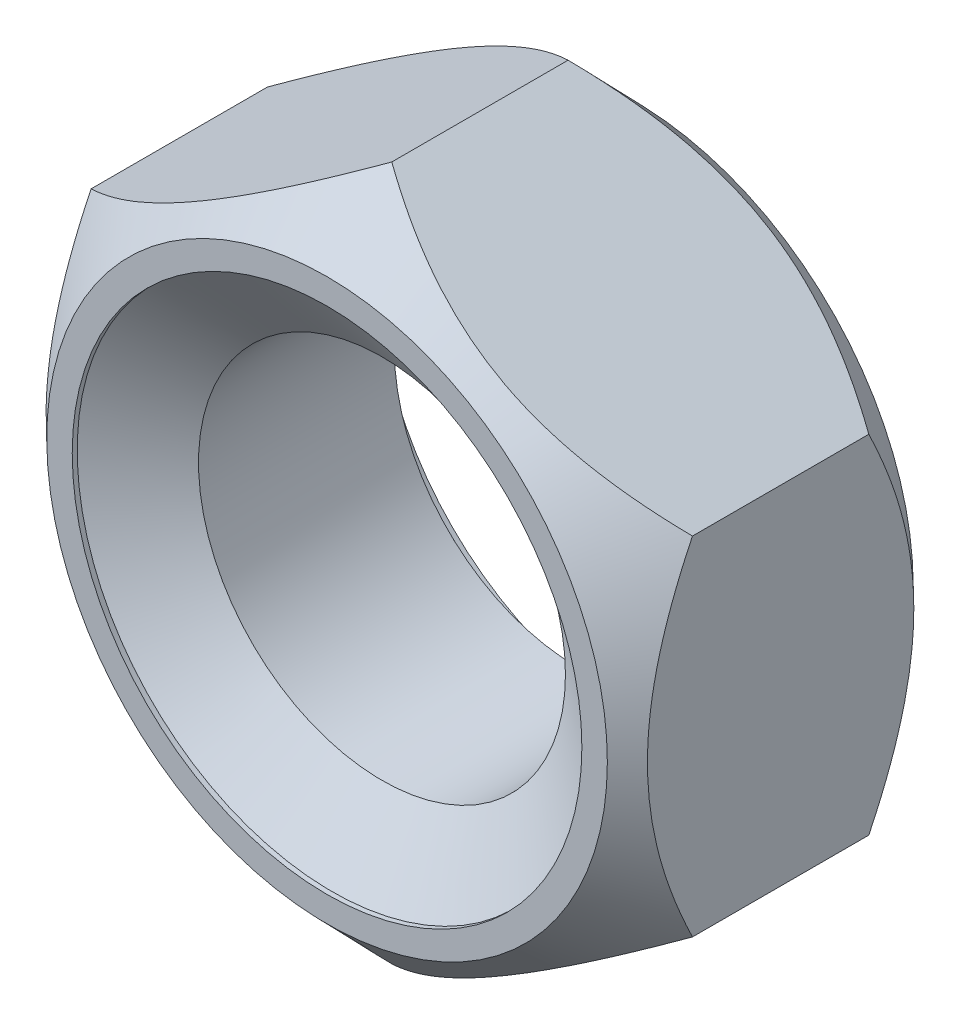
SolidWorks part; units mm, degrees
extrude "BaseNut" add sketch "BaseNutSke" against normal blind 3
sketch "BaseNutSke" plane through (0, 0, 0) normal (0, 0, 1) x (1, 0, 0)
  line L6 (2.95, 1.7032) -> (2.95, -1.7032)
  line L7 (-2.95, 1.7032) -> (-2.95, -1.7032)
  line L8 (2.95, 1.7032) -> (0, 3.4064)
  line L9 (0, 3.4064) -> (-2.95, 1.7032)
  line L10 (-2.95, -1.7032) -> (0, -3.4064)
  line L11 (0, -3.4064) -> (2.95, -1.7032)
  circle A0 centre (0, 0) radius 1.8
  dimension "Tap_drill" = 3.6
  dimension "Width_flats" = 5.9
  dimension "D2" = 2.95
  dimension "D3" = 2.95
  dimension "D1" = 120
  dimension "D4" = 2.95
pattern_linear "ThdSchPat" [suppressed]
revolve "ThreadSchematic" [suppressed] cut sketch "ThdSchSke" angle 360 about L6
sketch "ThdSchSke" plane through (0, 0, 0) normal (0, 1, 0) x (1, 0, 0)
  line L0 (-3.175, 0.0254) -> (-1.8, 0.9882)
  line L1 (-1.8, 0.9882) -> (-0.9, 0.9882)
  line L2 (-0.9, 0.9882) -> (-0.9, -0.9374)
  line L3 (-0.9, -0.9374) -> (-1.8, -0.9374)
  line L4 (-1.8, -0.9374) -> (-3.175, 0.0254)
  line L5 (-3.175, 1.27) -> (3.175, 1.27) construction
  line L6 (0, 1.27) -> (0, -2.9874) construction
  line L7 (0, 2.4601) -> (0, 0.5389) construction
  dimension "SideAngle" = 55
  dimension "Advance" = 1.27
  dimension "D1" = 0.0254
ref_plane "Plane1" through (0, 0, 0) normal (0, 0, 1) x (1, 0, 0)
ref_plane "Plane2" through (0, 0, 0) normal (0, 1, 0) x (1, 0, 0)
ref_plane "Plane3" through (0, 0, 0) normal (1, 0, 0) x (0, 0, -1)
sketch "Sketch4" plane through (0, 0, 0) normal (1, 0, 0) x (0, 0, -1)
  line L0 (3, 2.95) -> (2.5936, 2.95)
  line L1 (3, 2.95) -> (3, 16.1064)
  line L2 (2.5936, 16.1064) -> (3, 16.1064)
  line L3 (2.5936, 16.1064) -> (2.5936, 2.95)
  line L4 (0, 0) -> (34.925, 0) construction
  line L6 (3, 1.7032) -> (3, 3.4064) construction
  line L7 (0, 2.95) -> (-12.7, 2.95)
  line L8 (0, 1.7032) -> (0, 3.4064) construction
  line L9 (0.635, 3.4064) -> (0.635, 16.1064)
  line L10 (0.635, 16.1064) -> (-12.7, 16.1064)
  line L11 (-12.7, 16.1064) -> (-12.7, 2.95)
  line L12 (0, 2.95) -> (0.635, 3.4064)
  line L14 (0, 1.7032) -> (0, -1.7032) construction
  line L15 (3, 3.4064) -> (0, 3.4064) construction
  dimension "D2" = 0.635
  dimension "D3" = 12.7
  dimension "D4" = 12.7
  dimension "D1" = 2.95
revolve "Bearing-Face" [suppressed] cut sketch "Sketch4" angle 360 about L4
sketch "Sketch3" plane through (0, 0, 0) normal (1, 0, 0) x (0, 0, -1)
  line L0 (3, 2.75) -> (2.365, 3.4064)
  line L1 (2.365, 3.4064) -> (2.365, 16.1064)
  line L2 (2.365, 16.1064) -> (15.7, 16.1064)
  line L3 (15.7, 16.1064) -> (15.7, 2.75)
  line L4 (15.7, 2.75) -> (3, 2.75)
  line L5 (3, 1.7032) -> (3, 3.4064) construction
  line L6 (3, 3.4064) -> (0, 3.4064) construction
  line L7 (0, 0) -> (38.6776, 0) construction
  line L8 (3, 0) -> (0, 0) construction
  line L9 (1.5, 3.4064) -> (1.5, 44.222) construction
  line L10 (0.635, 16.1064) -> (-12.7, 16.1064)
  line L11 (-12.7, 16.1064) -> (-12.7, 2.75)
  line L12 (-12.7, 2.75) -> (0, 2.75)
  line L13 (0, 2.75) -> (0.635, 3.4064)
  line L14 (0.635, 3.4064) -> (0.635, 16.1064)
  line L16 (3, 3.4064) -> (0, 3.4064) construction
  dimension "D1" = 2.75
  dimension "D2" = 0.635
  dimension "D4" = 12.7
  dimension "D3" = 12.7
revolve "Double-Chamfer" cut sketch "Sketch3" angle 360 about L7
sketch "Sketch5" plane through (0, 0, 0) normal (1, 0, 0) x (0, 0, -1)
  line L0 (2.9502, 2.5) -> (1.8911, 0.9875)
  line L1 (3.001, 2.5) -> (2.9502, 2.5)
  line L2 (3.001, 2.5) -> (3.001, 0.9875)
  line L3 (3.001, 0.9875) -> (1.8911, 0.9875)
  line L6 (-0.002, 2.5) -> (0.0488, 2.5)
  line L7 (0.0488, 2.5) -> (1.1079, 0.9875)
  line L9 (1.1079, 0.9875) -> (-0.002, 0.9875)
  line L10 (-0.002, 0.9875) -> (-0.002, 2.5)
  line L11 (25.0375, 0) -> (38.388, 0) construction
  line L12 (3, 0) -> (0, 0) construction
  dimension "D1" = 35
  dimension "D2" = 0.0508
  dimension "ThreadMajor" = 2.5
  dimension "Offset1" = 3.001
revolve "EndChamfer" cut sketch "Sketch5" angle 360 about L11
equation "\"D2@BaseNutSke\"= \"Width_flats@BaseNutSke\" / 2"
equation "\"D3@BaseNutSke\" = \"Width_flats@BaseNutSke\" / 2"
equation "\"D1@Sketch3\"=\"Width_flats@BaseNutSke\" /2-0.2"
equation "\"D1@Sketch4\" = \"D2@BaseNutSke\""
equation "\"D4@BaseNutSke\" = \"D3@BaseNutSke\""
equation "\"Tap_Drill@ThdSchSke\" = \"Tap_drill@BaseNutSke\""
equation "\"OverCut@ThdSchSke\" = \"Tap_Drill@ThdSchSke\" * 0.5"
equation "\"Num_threads@ThdSchPat\" = int(  ( \"Thickness@BaseNut\" - 0.002 ) / \"Advance@ThdSchSke\" + 0.999 )  + 1"
equation "\"Advance@ThdSchPat\" = ( \"Thickness@BaseNut\" - 0.002 ) /  (\"Num_threads@ThdSchPat\" - 1) 'relax it"
equation "' \"Num_threads@ThdSchPat\" = \"Num_threads@ThdSchPat\" - sgn( \"Num_threads@ThdSchPat\" - 1) '---chamfered tips only---"
equation "\"Offset1@Sketch5\" = \"Thickness@BaseNut\" + 0.001"
equation "\"Offset2@Sketch5\" = \"Offset1@Sketch5\" + 0.002"
